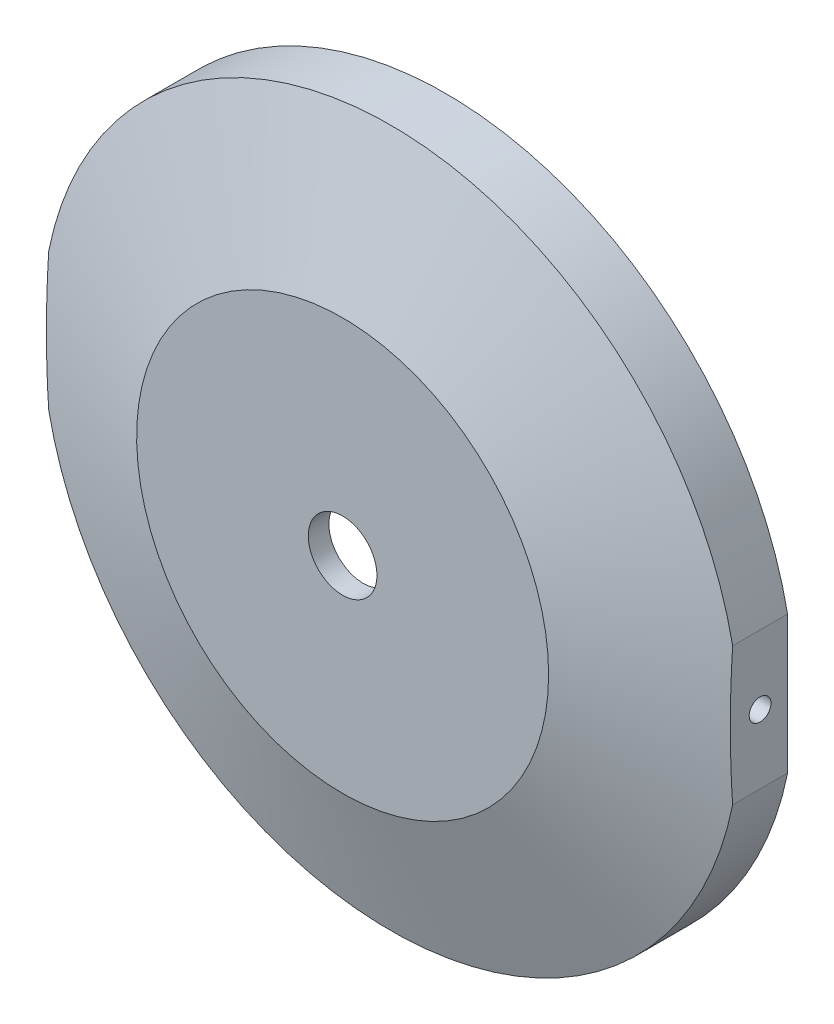
SolidWorks part; units mm, degrees
material "1060 Alloy"
ref_plane "Front Plane" through (0, 0, 0) normal (0, 0, 1) x (1, 0, 0)
ref_plane "Top Plane" through (0, 0, 0) normal (0, 1, 0) x (1, 0, 0)
ref_plane "Right Plane" through (0, 0, 0) normal (1, 0, 0) x (0, 0, -1)
sketch "Sketch2" plane through (0, 0, 0) normal (1, 0, 0) x (0, 0, -1)
  line L0 (0, 0) -> (0, 5) construction
  line L1 (0, 5) -> (3, 5)
  line L2 (3, 5) -> (3, 30)
  line L3 (3, 30) -> (15, 40.8)
  line L4 (15, 40.8) -> (15, 50.8)
  line L5 (15, 50.8) -> (7, 50.8)
  line L8 (0, 30) -> (0, 5)
  line L9 (0, 30) -> (7, 50.8)
  line L10 (-1000, 0) -> (49000, 0) construction
  dimension "D1" = 5
  dimension "D2" = 3
  dimension "D3" = 50.8
  dimension "D4" = 25
  dimension "D5" = 8
  dimension "D6" = 10
  dimension "D7" = 15
revolve "Revolve1" add sketch "Sketch2" angle 360 about L10
ref_plane "Plane1" through (50.8, 0, 0) normal (1, 0, 0) x (0, 0, -1)
sketch "Sketch5" plane through (50.8, 0, 0) normal (1, 0, 0) x (0, 0, -1)
  line L3 (22.5, -12.5) -> (-2.5, -12.5)
  line L4 (22.5, -12.5) -> (22.5, 12.5)
  line L5 (22.5, 12.5) -> (-2.5, 12.5)
  line L6 (-2.5, -12.5) -> (-2.5, 12.5)
  line L7 (22.5, -12.5) -> (-2.5, 12.5) construction
  line L8 (22.5, 12.5) -> (-2.5, -12.5) construction
  point P0 (10, 0)
  dimension "D1" = 10
  dimension "D2" = 25
extrude "Cut-Extrude3" cut sketch "Sketch5" against normal blind 1 contours L4 L3 L6 L5
sketch "Sketch6" plane through (49.8, 0, 0) normal (1, 0, 0) x (0, 0, -1)
  line L0 (7, 0) -> (15, 0) construction
  point P6 (11, 0)
  dimension "D1" = 8
hole_wizard "1/8 (0.125) Diameter Hole2" positions "3DSketch3" profile "Sketch7" hole size "1/8" standard "ANSI Inch"
sketch3d "3DSketch3"
  point P0 (49.8, 0, -11)
sketch "Sketch7" plane through (49.8, 0, -11) normal (0, 1, 0) x (0, 0, -1)
  line L0 (0, 0) -> (0, 12.6)
  line L1 (0, 12.6) -> (1.5875, 12.6)
  line L2 (1.5875, 12.6) -> (1.5875, 0)
  line L5 (1.5875, 0) -> (0, 0)
  line L11 (0, -6.35) -> (0, 107.95) construction
  dimension "Thru Hole Dia." = 3.175
  dimension "Thru Hole Depth" = 12.6
mirror "Mirror2" about plane through (0, 0, 0) normal (1, 0, 0) of "1/8 (0.125) Diameter Hole2", "Cut-Extrude3"
fillet "Fillet1" [suppressed] radius 4
fillet "Fillet2" [suppressed] radius 4
